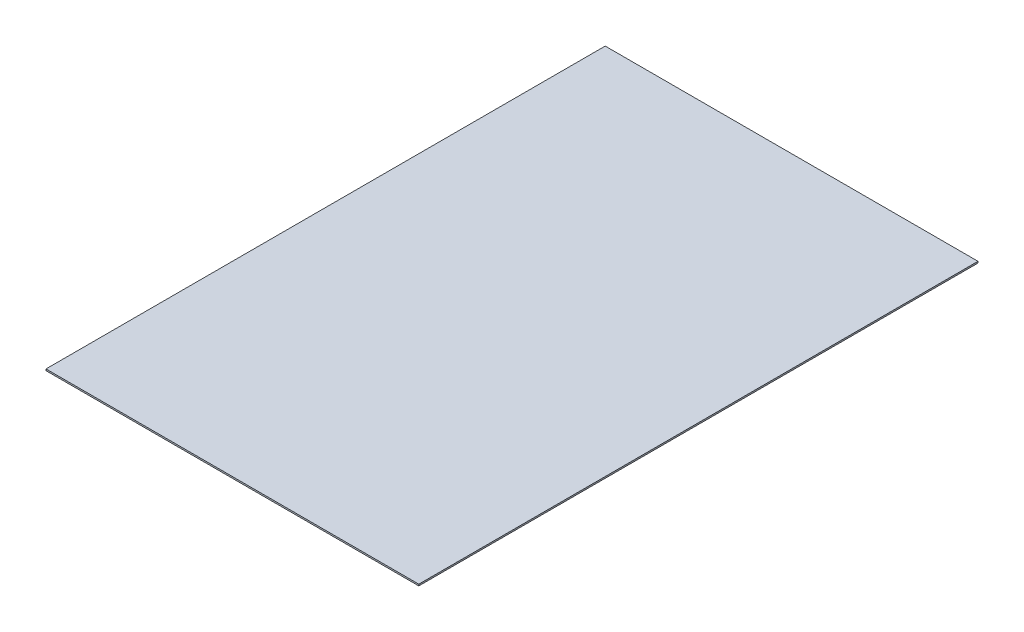
SolidWorks part; units mm, degrees
ref_plane "Front Plane" through (0, 0, 0) normal (0, 0, 1) x (1, 0, 0)
ref_plane "Top Plane" through (0, 0, 0) normal (0, 1, 0) x (1, 0, 0)
ref_plane "Right Plane" through (0, 0, 0) normal (1, 0, 0) x (0, 0, -1)
sketch "Sketch1" plane through (0, 0, 0) normal (0, 1, 0) x (1, 0, 0)
  line L1 (-381, -571.5) -> (381, -571.5)
  line L2 (-381, -571.5) -> (-381, 571.5)
  line L3 (-381, 571.5) -> (381, 571.5)
  line L4 (381, -571.5) -> (381, 571.5)
  line L5 (-381, -571.5) -> (381, 571.5) construction
  line L6 (-381, 571.5) -> (381, -571.5) construction
  point P0 (0, 0)
  dimension "D1" = 762
  dimension "D2" = 1143
extrude "Boss-Extrude1" add sketch "Sketch1" along normal blind 3.175 contours L4 L3 L2 L1
